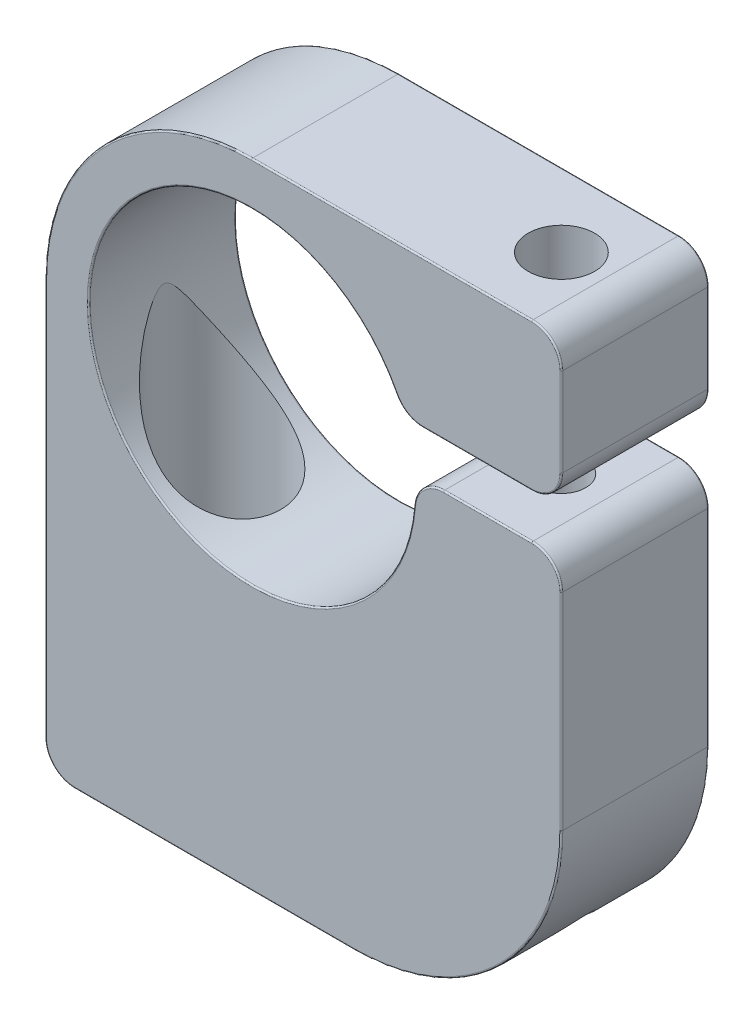
SolidWorks part; units mm, degrees
material "Сплав 2024"
ref_plane "Спереди" through (0, 0, 0) normal (0, 0, 1) x (1, 0, 0)
ref_plane "Сверху" through (0, 0, 0) normal (0, 1, 0) x (1, 0, 0)
ref_plane "Справа" through (0, 0, 0) normal (1, 0, 0) x (0, 0, -1)
sketch "Эскиз1" plane through (0, 0, 0) normal (0, 0, 1) x (1, 0, 0)
  line L0 (10.3006, 4) -> (21, 4)
  line L1 (0, 14) -> (21, 14)
  line L2 (-14, 0) -> (-14, -29)
  line L3 (-14, -29) -> (7, -29)
  line L4 (21, 14) -> (21, 4)
  line L5 (21, 1) -> (11.0047, 1)
  line L6 (21, 1) -> (21, -15)
  arc A0 (10.3006, 4) -> (11.0047, 1) centre (0, 0) ccw
  arc A1 (0, 14) -> (-14, 0) centre (0, 0) ccw
  arc A2 (7, -29) -> (21, -15) centre (7, -15) ccw
  dimension "D1" = 22.1
  dimension "D2" = 28
  dimension "D7" = 28
  dimension "D3" = 35
  dimension "D4" = 3
  dimension "D5" = 10
  dimension "D6" = 30
extrude "Бобышка-Вытянуть1" add sketch "Эскиз1" along normal blind 10
sketch "Эскиз2" plane through (0, 14, 0) normal (0, 1, 0) x (1, 0, 0)
  line L0 (21, -5) -> (1.7357, -5) construction
  line L1 (21, -10) -> (21, 0) construction
  line L2 (16, 0) -> (16, -10) construction
  line L3 (21, 0) -> (0, 0) construction
  line L4 (21, -10) -> (0, -10) construction
  dimension "D1" = 5
hole_wizard "Отверстие с зазором M41" positions "Эскиз4" profile "Эскиз3" hole size "M4" standard "Ansi Metric"
sketch "Эскиз4" plane through (0, 14, 0) normal (0, 1, 0) x (1, 0, 0)
  line L0 (16, 0) -> (16, -10) construction
  point P0 (16, -5)
sketch "Эскиз3" plane through (16, 14, 5) normal (1, 0, 0) x (0, 0, 1)
  line L0 (0, 0) -> (0, 5.3519)
  line L1 (0, 5.3519) -> (2.25, 4)
  line L2 (2.25, 4) -> (2.25, 0)
  line L5 (2.25, 0) -> (0, 0)
  line L10 (0, 5.3519) -> (-2.25, 4) construction
  line L11 (0, -6.35) -> (0, 107.95) construction
  dimension "Диаметр отверстия" = 4.5
  dimension "Глубина отверстия" = 4
  dimension "Угол заточки сверла" = 118
hole_wizard "Отверстие обработанное метчиком M4x0.71" positions "Эскиз6" profile "Эскиз5" tap size "M4x0.7" standard "Ansi Metric"
sketch "Эскиз6" plane through (0, 1, 0) normal (0, 1, 0) x (1, 0, 0)
  line L0 (16, 0) -> (16, -10) construction
  point P0 (16, -5)
sketch "Эскиз5" plane through (16, 1, 5) normal (1, 0, 0) x (0, 0, 1)
  line L0 (0, 0) -> (0, 30)
  line L1 (0, 30) -> (1.65, 30)
  line L2 (1.65, 30) -> (1.65, 0)
  line L5 (1.65, 0) -> (0, 0)
  line L11 (0, -6.35) -> (0, 107.95) construction
  dimension "Диаметр проходного сверла" = 3.3
  dimension "Глубина проходного сверла" = 30
cosmetic thread "Отверстие резьбы1" parameters "D2"=4
sketch "Эскиз7" plane through (0, -29, 0) normal (0, -1, 0) x (1, 0, 0)
  line L0 (-14, 5) -> (0, 5) construction
  line L1 (-14, 10) -> (-14, 0) construction
  line L2 (-7, 10) -> (-7, 0) construction
  line L3 (-14, 10) -> (7, 10) construction
  line L4 (-14, 0) -> (7, 0) construction
  dimension "D1" = 7
hole_wizard "Отверстие обработанное метчиком 3/8-161" positions "Эскиз9" profile "Эскиз8" tap size "3/8-16" standard "Ansi Inch"
sketch "Эскиз9" plane through (0, -29, 0) normal (0, -1, 0) x (-1, 0, 0)
  line L0 (14, -5) -> (0, -5) construction
  point P0 (7, -5)
sketch "Эскиз8" plane through (-7, -29, 5) normal (1, 0, 0) x (0, 0, -1)
  line L0 (0, 0) -> (0, 20.45)
  line L1 (0, 20.45) -> (3.9687, 20.45)
  line L2 (3.9687, 20.45) -> (3.9687, 0)
  line L5 (3.9687, 0) -> (0, 0)
  line L11 (0, -6.35) -> (0, 107.95) construction
  dimension "Диаметр проходного сверла" = 7.9375
  dimension "Глубина проходного сверла" = 20.45
cosmetic thread "Отверстие резьбы2" parameters "D2"=9.525
fillet "Скругление1" radius 2 6 edges at (-14, -29, 5) (21, 14, 5) (21, 4, 5) (21, 1, 5) (11.0047, 1, 5) (10.3006, 4, 5)
fillet "Скругление2" radius 0.1 32 edges at (-9.8995, 9.8995, 10) (9.5, 14, 10) (20.4142, 13.4142, 10) (21, 9, 10) (20.4142, 4.5858, 10) (15.2944, 4, 10) (10.5494, 4.2913, 10) (-10.8286, -2.2009, 10) (11.6527, 0.4674, 10) (16.0058, 1, 10) (20.4142, 0.4142, 10) (21, -8, 10) (16.8995, -24.8995, 10) (-2.5, -29, 10) (-13.4142, -28.4142, 10) (-14, -13.5, 10) (16.8995, -24.8995, 0) (21, -8, 0) (20.4142, 0.4142, 0) (16.0058, 1, 0) (11.6527, 0.4674, 0) (-10.8286, -2.2009, 0) (10.5494, 4.2913, 0) (15.2944, 4, 0) (20.4142, 4.5858, 0) (21, 9, 0) (20.4142, 13.4142, 0) (9.5, 14, 0) (-9.8995, 9.8995, 0) (-14, -13.5, 0) (-13.4142, -28.4142, 0) (-2.5, -29, 0)
